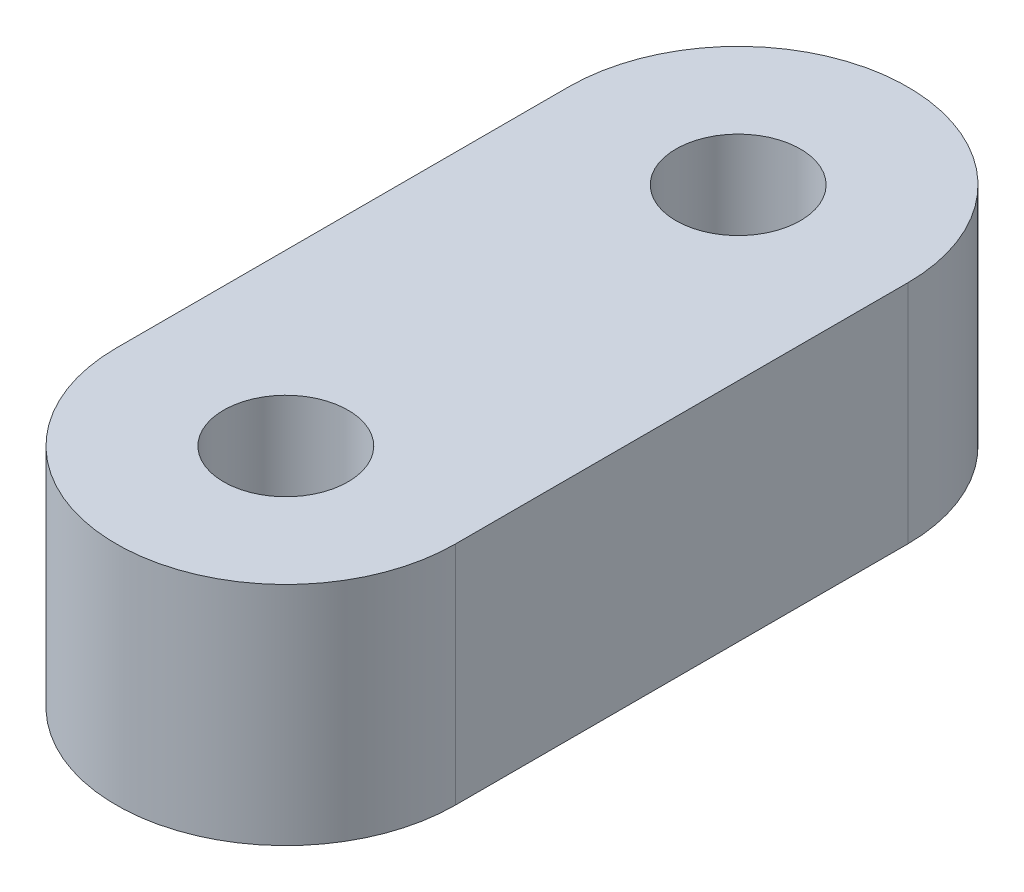
SolidWorks part; units mm, degrees
ref_plane "Front Plane" through (0, 0, 0) normal (0, 0, 1) x (1, 0, 0)
ref_plane "Top Plane" through (0, 0, 0) normal (0, 1, 0) x (1, 0, 0)
ref_plane "Right Plane" through (0, 0, 0) normal (1, 0, 0) x (0, 0, -1)
sketch "Sketch1" plane through (0, 0, 0) normal (0, 1, 0) x (1, 0, 0)
  line L0 (0, 0) -> (0, 20)
  line L1 (0, 20) -> (0, 0) construction
  line L2 (7.5, 20) -> (7.5, 0)
  line L3 (-7.5, 20) -> (-7.5, 0)
  circle A0 centre (0, 20) radius 2.75
  circle A1 centre (0, 0) radius 2.75
  arc A2 (7.5, 20) -> (-7.5, 20) centre (0, 20) ccw
  arc A3 (-7.5, 0) -> (7.5, 0) centre (0, 0) ccw
  point P5 (0, 10)
extrude "Boss-Extrude1" add sketch "Sketch1" along normal blind 10
